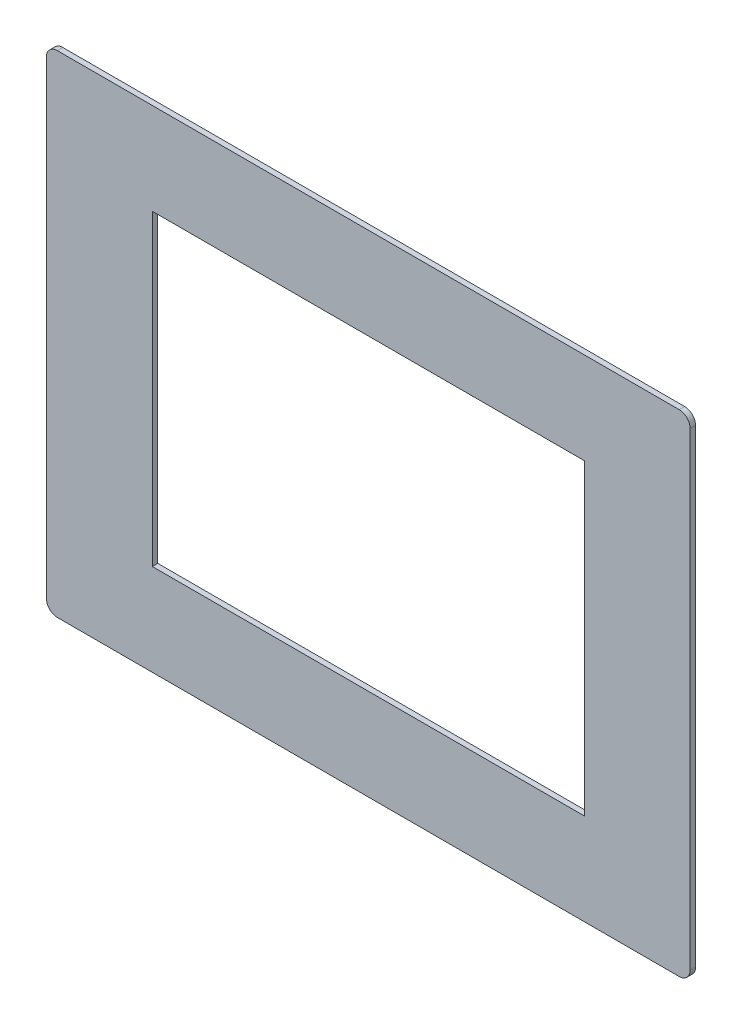
SolidWorks part; units mm, degrees
ref_plane "Front Plane" through (0, 0, 0) normal (0, 0, 1) x (1, 0, 0)
ref_plane "Top Plane" through (0, 0, 0) normal (0, 1, 0) x (1, 0, 0)
ref_plane "Right Plane" through (0, 0, 0) normal (1, 0, 0) x (0, 0, -1)
sketch "Sketch1" plane through (0, 0, 0) normal (0, 0, 1) x (1, 0, 0)
  line L1 (-147.5, -112.5) -> (147.5, -112.5)
  line L2 (-147.5, -112.5) -> (-147.5, 112.5)
  line L3 (-147.5, 112.5) -> (147.5, 112.5)
  line L4 (147.5, -112.5) -> (147.5, 112.5)
  line L5 (-147.5, -112.5) -> (147.5, 112.5) construction
  line L6 (-147.5, 112.5) -> (147.5, -112.5) construction
  line L7 (-99, -70.5) -> (99, -70.5)
  line L8 (-99, -70.5) -> (-99, 70.5)
  line L9 (-99, 70.5) -> (99, 70.5)
  line L10 (99, -70.5) -> (99, 70.5)
  line L11 (-99, -70.5) -> (99, 70.5) construction
  line L12 (-99, 70.5) -> (99, -70.5) construction
  point P0 (0, 0)
  point P6 (0, 0)
  dimension "D1" = 295
  dimension "D2" = 225
  dimension "D3" = 198
  dimension "D4" = 141
extrude "Boss-Extrude1" add sketch "Sketch1" along normal blind 2.5
fillet "Fillet1" radius 5 4 edges at (-147.5, -112.5, 1.25) (147.5, -112.5, 1.25) (147.5, 112.5, 1.25) (-147.5, 112.5, 1.25)
